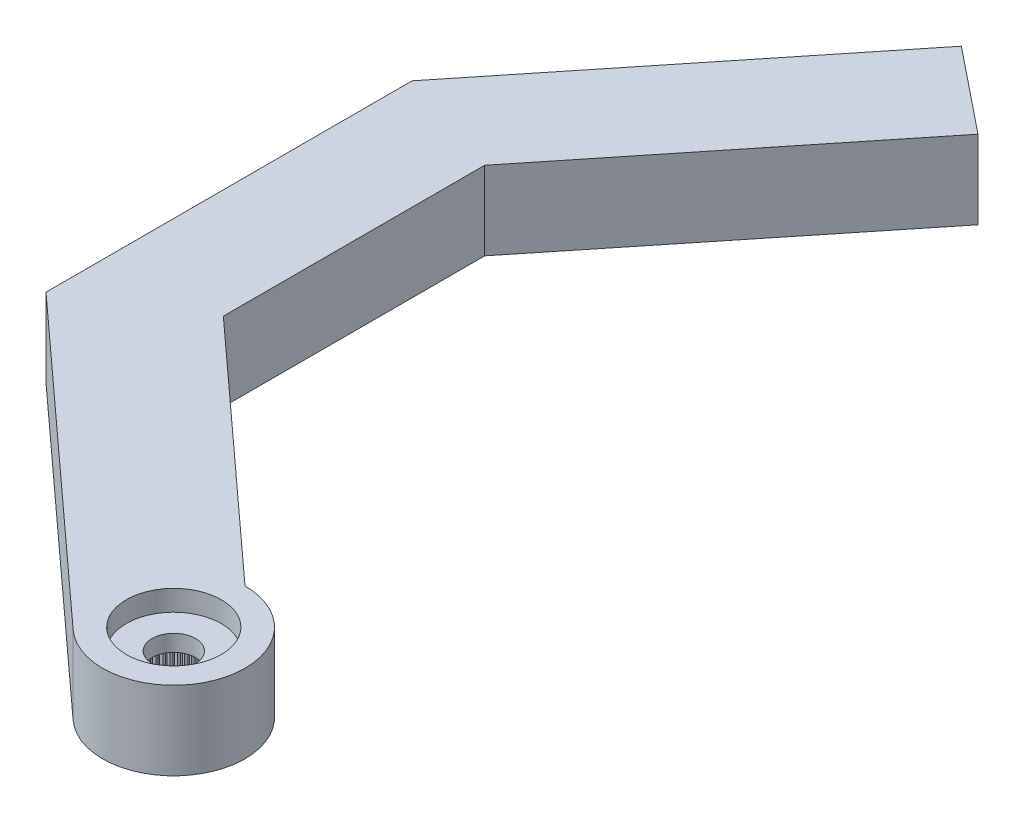
SolidWorks part; units mm, degrees
material "PVC Rígido"
ref_plane "Plano frontal" through (0, 0, 0) normal (0, 0, 1) x (1, 0, 0)
ref_plane "Plano superior" through (0, 0, 0) normal (0, 1, 0) x (1, 0, 0)
ref_plane "Plano direito" through (0, 0, 0) normal (1, 0, 0) x (0, 0, -1)
sketch "Esboço1" plane through (0, 0, 0) normal (0, 1, 0) x (1, 0, 0)
  line L0 (0, 0) -> (-14.05, 0) construction
  line L1 (-14.1591, 1.997) -> (-2.2091, 2.65)
  line L2 (-2.2091, -2.65) -> (-14.1591, -1.997)
  arc A0 (-2.2091, -2.65) -> (-2.2091, 2.65) centre (0, 0) ccw
  arc A1 (-14.1591, 1.997) -> (-14.1591, -1.997) centre (-14.05, 0) ccw
  dimension "D1" = 6.9
  dimension "D2" = 4
  dimension "D3" = 19.5
  dimension "D4" = 5.3
extrude "Ressalto-extrusão1" add sketch "Esboço1" against normal blind 1.4
sketch "Esboço2" plane through (0, -1.4, 0) normal (0, -1, 0) x (1, 0, 0)
  arc A0 (-2.2091, -2.65) -> (-2.2091, 2.65) centre (0, 0) ccw construction
  circle A1 centre (0, 0) radius 3.45
extrude "Ressalto-extrusão2" add sketch "Esboço2" along normal offset from surface (2.4 mm away) 3.8 up to face at (-7.242, 0, 0)
hole_wizard "Furo4" positions "Esboço9" profile "Esboço10" legacy end condition through all
sketch "Esboço9" plane through (0, 0, 0) normal (0, 1, 0) x (1, 0, 0)
  line L1 (-14.45, 0) -> (0, 0) construction
  arc A2 (-14.1591, 1.997) -> (-14.1591, -1.997) centre (-14.05, 0) ccw construction
  point P0 (-14.45, 0)
  point P19 (-16.05, 0)
  dimension "D1" = 1.6
sketch "Esboço10" plane through (-14.45, 0, 0) normal (1, 0, 0) x (0, 0, 1)
  line L0 (0, 0) -> (0, 3.8)
  line L1 (0, 3.8) -> (0.6, 3.8)
  line L2 (0.6, 3.8) -> (0.6, 0)
  line L3 (0.6, 0) -> (0, 0)
  line L4 (0, 110) -> (0, -10) construction
  dimension "Diameter" = 1.2
  dimension "Depth" = 3.8
pattern_linear "Padrão linear1" count 6 spacing 2 along (1, 0, 0) of "Furo4"
hole_wizard "Furo1" positions "Esboço3" profile "Esboço4" legacy
sketch "Esboço3" plane through (0, -3.8, 0) normal (0, -1, 0) x (-1, 0, 0)
  point P0 (0, 0)
sketch "Esboço4" plane through (0, -3.8, 0) normal (1, 0, 0) x (0, 0, -1)
  line L0 (0, 0) -> (0, 2)
  line L1 (0, 2) -> (2.475, 2)
  line L2 (2.475, 2) -> (2.475, 0)
  line L3 (2.475, 0) -> (0, 0)
  line L4 (0, 110) -> (0, -10) construction
  dimension "Diameter" = 4.95
  dimension "Depth" = 2
hole_wizard "Furo2" positions "Esboço5" profile "Esboço6" legacy
sketch "Esboço5" plane through (0, 0, 0) normal (0, 1, 0) x (1, 0, 0)
  point P0 (0, 0)
sketch "Esboço6" plane through (0, 0, 0) normal (1, 0, 0) x (0, 0, 1)
  line L0 (0, 0) -> (0, 1)
  line L1 (0, 1) -> (2.3, 1)
  line L2 (2.3, 1) -> (2.3, 0)
  line L3 (2.3, 0) -> (0, 0)
  line L4 (0, 110) -> (0, -10) construction
  dimension "Diameter" = 4.6
  dimension "Depth" = 1
hole_wizard "Furo3" positions "Esboço7" profile "Esboço8" legacy end condition through all
sketch "Esboço7" plane through (0, 0, 0) normal (0, 1, 0) x (1, 0, 0)
  point P0 (0, 0)
sketch "Esboço8" plane through (0, 0, 0) normal (1, 0, 0) x (0, 0, 1)
  line L0 (0, 0) -> (0, 3.8)
  line L1 (0, 3.8) -> (1.05, 3.8)
  line L2 (1.05, 3.8) -> (1.05, 0)
  line L3 (1.05, 0) -> (0, 0)
  line L4 (0, 110) -> (0, -10) construction
  dimension "Diameter" = 2.1
  dimension "Depth" = 3.8
sketch "Esboço11" plane through (0, -3.8, 0) normal (0, -1, 0) x (1, 0, 0)
  line L0 (-0.0981, 2.4731) -> (0, 2.375)
  line L1 (0, 2.375) -> (0.0981, 2.4731)
  line L2 (0, 0) -> (0, 2.475) construction
  circle A0 centre (0, 0) radius 2.375 construction
  circle A1 centre (0, 0) radius 2.475
  arc A2 (0.0981, 2.4731) -> (-0.0981, 2.4731) centre (0, 0) ccw
  dimension "D3" = 4.75
  dimension "D2" = 0.1
  dimension "D1" = 0
extrude "Ressalto-extrusão3" add sketch "Esboço11" against normal up to surface (2 mm away) up to face at (0, -1.8, 1.05)
pattern_circular "PadrãoCircular1" count 60 over 360 about axis through (0, 0, 0) along (0, 1, 0) of "Ressalto-extrusão3"
sketch "Sketch1" plane through (0, -3.8, 0) normal (0, -1, 0) x (1, 0, 0)
  line L0 (0, 3.45) -> (-16.05, 3.45)
  line L1 (-16.05, 3.45) -> (-16.05, -3.45)
  line L2 (-16.05, -3.45) -> (0, -3.45)
  arc A0 (0, 3.45) -> (0, -3.45) centre (0, 0) ccw
  circle A1 centre (0, 0) radius 3.45 construction
  arc A2 (-14.1591, 1.997) -> (-14.1591, -1.997) centre (-14.05, 0) ccw construction
  point P13 (-1.7998, -2.9434)
  point P14 (0, 0)
extrude "Cut-Extrude1" cut sketch "Sketch1" against normal blind 10
sketch "Sketch2" plane through (0, 0, 0) normal (0, 1, 0) x (1, 0, 0)
  line L0 (0, 3.45) -> (-11.8414, 14.241)
  line L1 (-11.8414, 14.241) -> (-11.8414, 26.8984)
  line L2 (-11.8414, 26.8984) -> (-1.2003, 40.1475)
  line L3 (-1.2003, 40.1475) -> (-5.2937, 43.4351)
  line L4 (-5.2937, 43.4351) -> (-17.1414, 28.6838)
  line L5 (-17.1414, 28.6838) -> (-17.1414, 10.9532)
  line L6 (-17.1414, 10.9532) -> (-2.3238, -2.55)
  circle A0 centre (0, 0) radius 3.45
  arc A1 (0, 3.45) -> (-2.3238, -2.55) centre (0, 0) ccw
  circle A2 centre (0, 0) radius 3.45 construction
  point P11 (-11.8414, 14.241)
  dimension "D1" = 17.7306
  dimension "D2" = 6
  dimension "D3" = 5.2502
  dimension "D4" = 5.3
  dimension "D5" = 141.23
  dimension "D6" = 20.0474
extrude "Boss-Extrude1" add sketch "Sketch2" against normal up to surface (3.8 mm away) contours L6 A1 L0 L1 L2 L3 L4 L5 up to face at (0, -3.8, 0)
